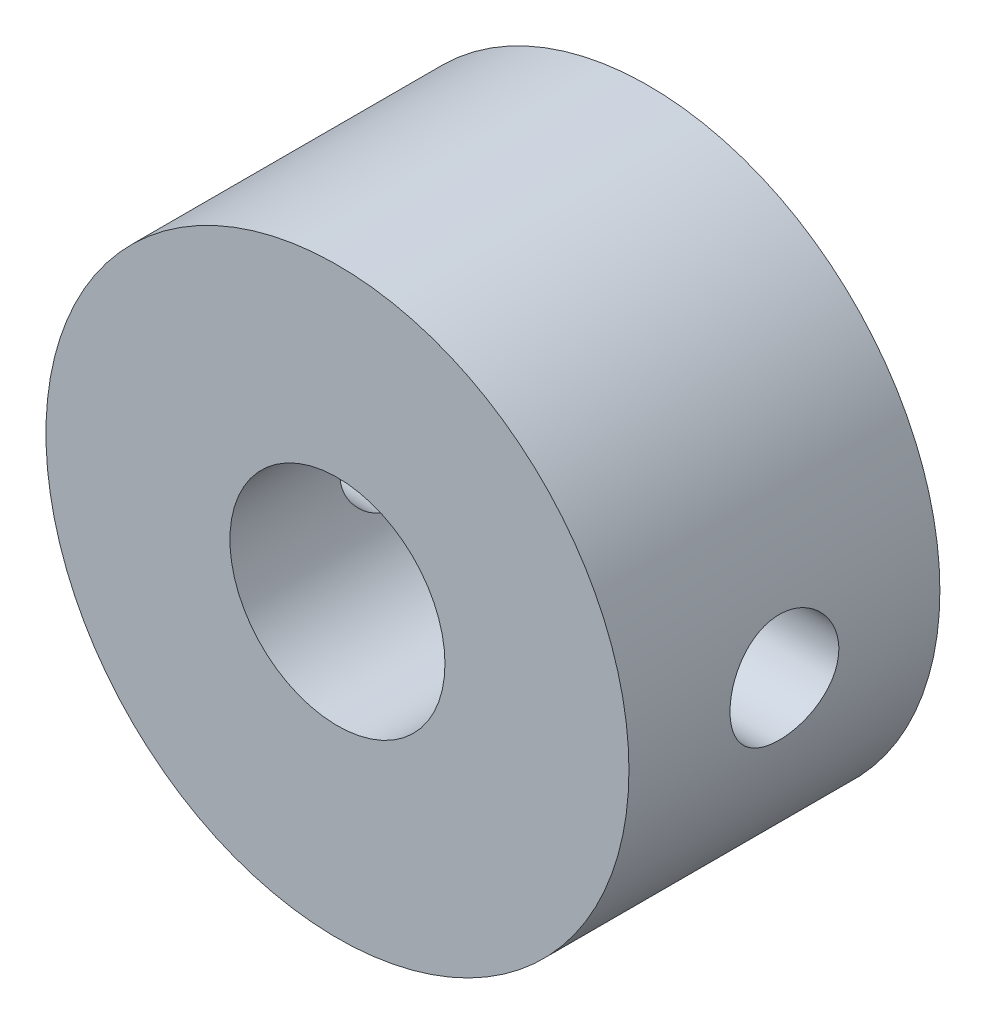
SolidWorks part; units mm, degrees
ref_plane "Front Plane" through (0, 0, 0) normal (0, 0, 1) x (1, 0, 0)
ref_plane "Top Plane" through (0, 0, 0) normal (0, 1, 0) x (1, 0, 0)
ref_plane "Right Plane" through (0, 0, 0) normal (1, 0, 0) x (0, 0, -1)
sketch "Sketch1" plane through (0, 0, 0) normal (0, 0, 1) x (1, 0, 0)
  circle A0 centre (0, 0) radius 11.25
  dimension "D1" = 22.5
extrude "Boss-Extrude1" add sketch "Sketch1" along normal blind 12
sketch "Sketch2" plane through (0, 0, 12) normal (0, 0, 1) x (1, 0, 0)
  circle A0 centre (0, 0) radius 4.15
  dimension "D1" = 8.3
extrude "Cut-Extrude1" cut sketch "Sketch2" against normal blind 15
ref_plane "Plane1" through (-11.25, 0, 0) normal (-1, 0, 0) x (0, 0, 1)
sketch "Sketch3" plane through (-11.25, 0, 0) normal (1, 0, 0) x (0, 0, -1)
  line L0 (-12, 0) -> (0, 0) construction
  line L1 (-12, 11.25) -> (-12, -11.25) construction
  line L2 (0, -11.25) -> (0, 11.25) construction
  circle A0 centre (-6, 0) radius 2.1
  dimension "D1" = 4.2
extrude "Cut-Extrude2" cut sketch "Sketch3" along normal blind 5
sketch "Sketch4" plane through (-6.25, 0, 0) normal (-1, 0, 0) x (0, 0, 1)
  circle A0 centre (6, 0) radius 1.75
  dimension "D1" = 3.5
extrude "Cut-Extrude3" cut sketch "Sketch4" against normal through all
mirror "Mirror1" about plane through (0, 0, 0) normal (1, 0, 0) of "Cut-Extrude2"
